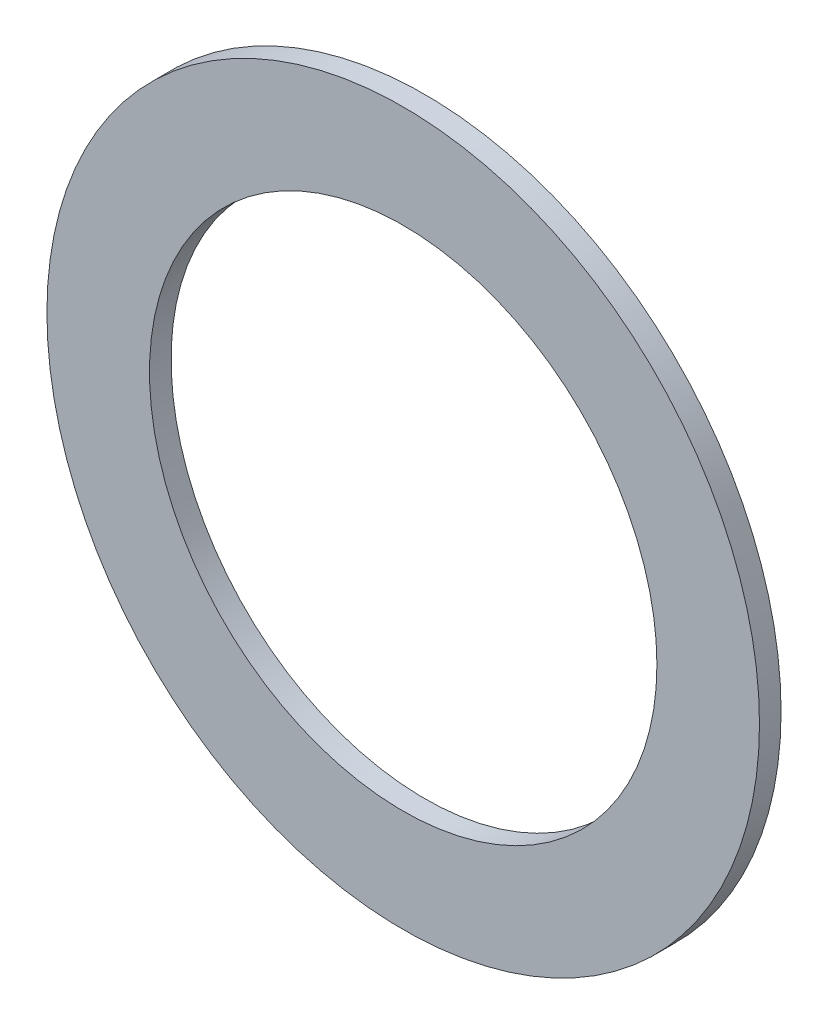
SolidWorks part; units mm, degrees
ref_plane "Plane1" through (0, 0, 0) normal (0, 0, 1) x (1, 0, 0)
ref_plane "Plane2" through (0, 0, 0) normal (0, 1, 0) x (1, 0, 0)
ref_plane "Plane3" through (0, 0, 0) normal (1, 0, 0) x (0, 0, -1)
sketch "Sketch1" plane through (0, 0, 0) normal (0, 0, 1) x (1, 0, 0)
  circle A0 centre (0, 0) radius 5.969 construction
  circle A1 centre (0, 0) radius 8.382
  circle A2 centre (0, 0) radius 8.382
  circle A3 centre (0, 0) radius 5.969
  dimension "D1" = 0
extrude "Base-Extrude" add sketch "Sketch1" along normal blind 0.508
